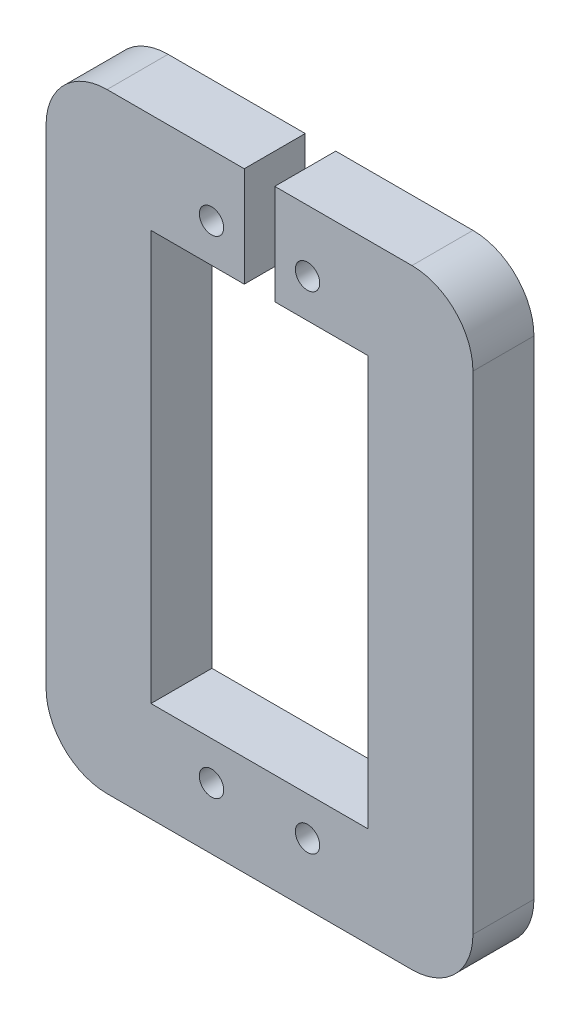
SolidWorks part; units mm, degrees
ref_plane "Front Plane" through (0, 0, 0) normal (0, 0, 1) x (1, 0, 0)
ref_plane "Top Plane" through (0, 0, 0) normal (0, 1, 0) x (1, 0, 0)
ref_plane "Right Plane" through (0, 0, 0) normal (1, 0, 0) x (0, 0, -1)
sketch "Sketch1" plane through (0, 0, 0) normal (0, 0, 1) x (1, 0, 0)
  line L0 (-4.9998, 25.3514) -> (4.9998, -25.3514) construction
  line L1 (-22.225, 31.75) -> (22.225, 31.75)
  line L2 (-22.225, 31.75) -> (-22.225, -31.75)
  line L3 (-22.225, -31.75) -> (22.225, -31.75)
  line L4 (22.225, 31.75) -> (22.225, -31.75)
  line L5 (-22.225, -31.75) -> (22.225, 31.75) construction
  circle A0 centre (-4.9998, 25.3514) radius 1.27
  circle A1 centre (4.9996, 25.3508) radius 1.27
  circle A2 centre (-5.0004, -25.3523) radius 1.27
  circle A3 centre (4.9998, -25.3514) radius 1.27
  point P12 (0, 0)
  point P13 (0, 0)
  dimension "D1" = 2.54
  dimension "D2" = 44.45
  dimension "D3" = 63.5
extrude "Boss-Extrude1" add sketch "Sketch1" along normal blind 6.35
sketch "Sketch2" plane through (0, 0, 6.35) normal (0, 0, 1) x (1, 0, 0)
  line L0 (-22.225, 31.75) -> (22.225, -31.75) construction
  line L2 (-11.303, -21.336) -> (11.303, -21.336)
  line L3 (-11.303, -21.336) -> (-11.303, 21.336)
  line L4 (-11.303, 21.336) -> (11.303, 21.336)
  line L5 (11.303, -21.336) -> (11.303, 21.336)
  line L6 (-11.303, -21.336) -> (11.303, 21.336) construction
  line L7 (-11.303, 21.336) -> (11.303, -21.336) construction
  point P4 (0, 0)
  point P5 (0, 0)
  dimension "D1" = 22.606
  dimension "D2" = 42.672
extrude "Cut-Extrude1" cut sketch "Sketch2" against normal through all
sketch "Sketch3" plane through (0, 0, 6.35) normal (0, 0, 1) x (1, 0, 0)
  line L1 (-1.5875, 35.3399) -> (1.5875, 35.3399)
  line L2 (-1.5875, 35.3399) -> (-1.5875, 19.0914)
  line L3 (-1.5875, 19.0914) -> (1.5875, 19.0914)
  line L4 (1.5875, 35.3399) -> (1.5875, 19.0914)
  line L5 (-1.5875, 35.3399) -> (1.5875, 19.0914) construction
  line L6 (-1.5875, 19.0914) -> (1.5875, 35.3399) construction
  point P0 (0, 27.2156)
  dimension "D1" = 3.175
extrude "Cut-Extrude2" cut sketch "Sketch3" against normal through all
fillet "Fillet1" radius 6.35 4 edges at (22.225, -31.75, 3.175) (-22.225, -31.75, 3.175) (22.225, 31.75, 3.175) (-22.225, 31.75, 3.175)
